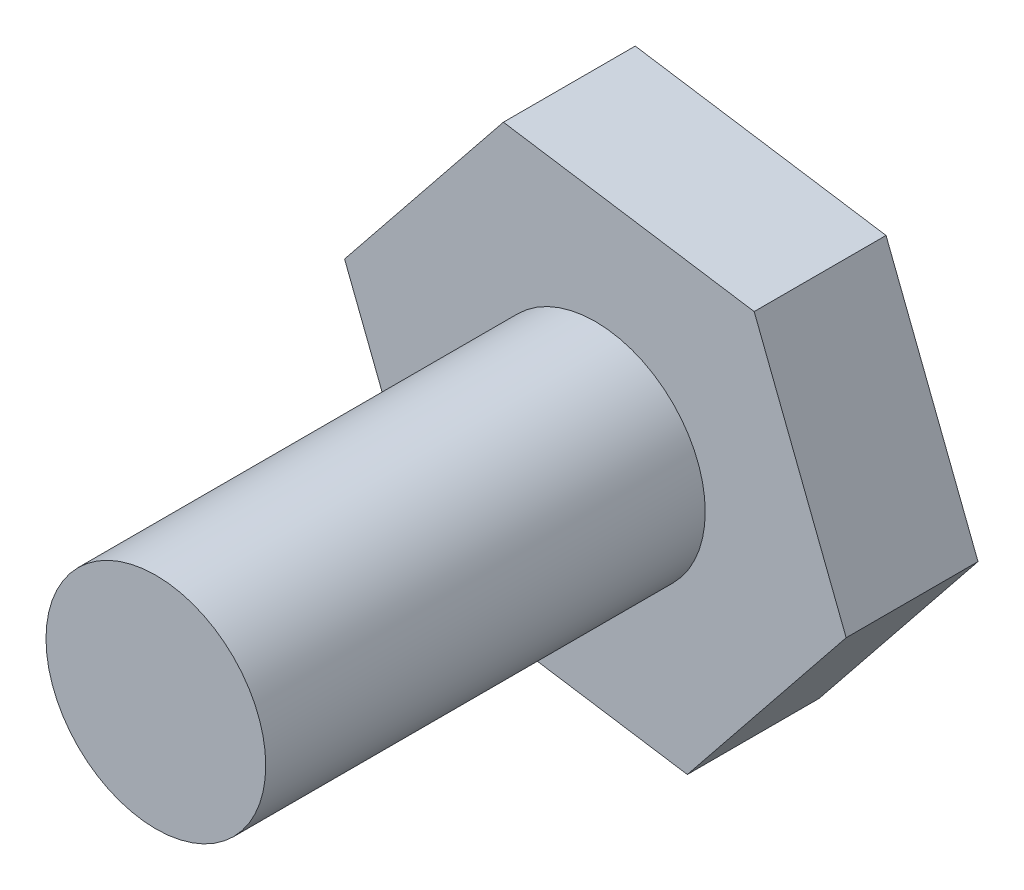
SolidWorks part; units mm, degrees
ref_plane "Alzado" through (0, 0, 0) normal (0, 0, 1) x (1, 0, 0)
ref_plane "Planta" through (0, 0, 0) normal (0, 1, 0) x (1, 0, 0)
ref_plane "Vista lateral" through (0, 0, 0) normal (1, 0, 0) x (0, 0, -1)
sketch "Croquis1" plane through (0, 0, 0) normal (0, 0, 1) x (1, 0, 0)
  line L1 (-54.3866, 4.2999) -> (-50.7729, 8.8026)
  line L2 (-50.7729, 8.8026) -> (-52.8655, 14.1835)
  line L3 (-52.8655, 14.1835) -> (-58.5718, 15.0617)
  line L4 (-58.5718, 15.0617) -> (-62.1855, 10.559)
  line L5 (-62.1855, 10.559) -> (-60.093, 5.1781)
  line L6 (-60.093, 5.1781) -> (-54.3866, 4.2999)
  circle A0 centre (-56.4792, 9.6808) radius 5 construction
  dimension "D1" = 5
extrude "Saliente-Extruir3" add sketch "Croquis1" along normal blind 3
sketch "Croquis3" plane through (0, 0, 0) normal (0, 0, 1) x (1, 0, 0)
  line L0 (-52.8655, 14.1835) -> (-58.5718, 15.0617) construction
  line L1 (-62.1855, 10.559) -> (-60.093, 5.1781) construction
  circle A0 centre (-56.4792, 9.6808) radius 2.5
  dimension "D1" = 5
  dimension "D2" = 5
extrude "Saliente-Extruir4" add sketch "Croquis3" along normal blind 13
